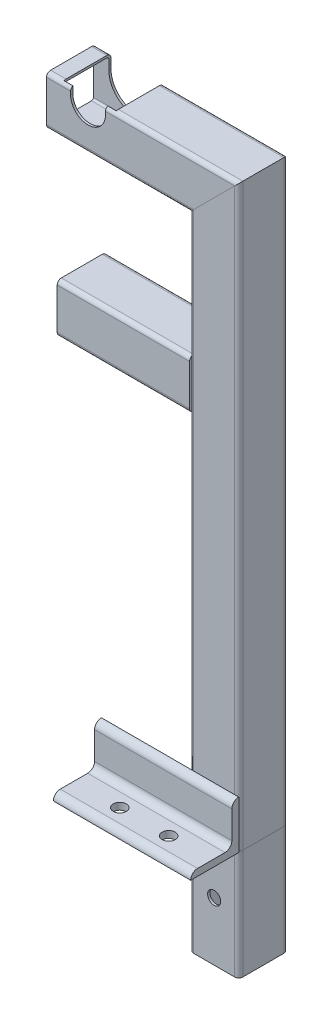
SolidWorks part; units mm, degrees
ref_plane "Front Plane" through (0, 0, 0) normal (0, 0, 1) x (1, 0, 0)
ref_plane "Top Plane" through (0, 0, 0) normal (0, 1, 0) x (1, 0, 0)
ref_plane "Right Plane" through (0, 0, 0) normal (1, 0, 0) x (0, 0, -1)
sketch "Sketch1" plane through (0, 0, 0) normal (0, 0, 1) x (1, 0, 0)
  line L0 (276.8375, 0) -> (276.8375, 404)
  line L1 (276.8375, 404) -> (154.7375, 404)
  line L2 (276.8375, 0) -> (276.8375, -80)
  line L3 (258.9375, 157.0549) -> (258.9375, -80) construction
  line L4 (263.7, 157.0549) -> (263.7, -80) construction
  line L5 (276.8375, 157.0549) -> (276.8375, -80) construction
  line L6 (276.8375, 276.9) -> (162.5375, 276.9)
  dimension "D1" = 404
  dimension "D2" = 80
  dimension "D3" = 122.1
  dimension "D4" = 4.7625
  dimension "D5" = 17.9
  dimension "D6" = 263.7
  dimension "D7" = 276.9
  dimension "D8" = 114.3
other "Structural MemberMain"
ref_plane "Plane1" through (276.8375, 0, 0) normal (0, 1, 0) x (-1, 0, 0)
sketch "Sketch11" plane through (276.8375, 0, 0) normal (0, 1, 0) x (-1, 0, 0)
  line L0 (-14.9, 16.3) -> (14.9, 16.3)
  line L1 (-14.9, 17.9) -> (14.9, 17.9)
  line L2 (-17.9, 14.9) -> (-17.9, -14.9)
  line L3 (-14.9, -17.9) -> (14.9, -17.9)
  line L4 (17.9, 14.9) -> (17.9, -14.9)
  line L5 (-17.9, 17.9) -> (17.9, -17.9) construction
  line L6 (-17.9, -17.9) -> (17.9, 17.9) construction
  line L7 (16.3, 14.9) -> (16.3, -14.9)
  line L8 (-14.9, -16.3) -> (14.9, -16.3)
  line L9 (-16.3, 14.9) -> (-16.3, -14.9)
  arc A0 (-17.9, -14.9) -> (-14.9, -17.9) centre (-14.9, -14.9) ccw
  arc A1 (14.9, -17.9) -> (17.9, -14.9) centre (14.9, -14.9) ccw
  arc A2 (17.9, 14.9) -> (14.9, 17.9) centre (14.9, 14.9) ccw
  arc A3 (-14.9, 17.9) -> (-17.9, 14.9) centre (-14.9, 14.9) ccw
  arc A4 (16.3, 14.9) -> (14.9, 16.3) centre (14.9, 14.9) ccw
  arc A5 (14.9, -16.3) -> (16.3, -14.9) centre (14.9, -14.9) ccw
  arc A6 (-16.3, -14.9) -> (-14.9, -16.3) centre (-14.9, -14.9) ccw
  arc A7 (-14.9, 16.3) -> (-16.3, 14.9) centre (-14.9, 14.9) ccw
  point P0 (0, 0)
  point P30 (0, 0)
  dimension "D3" = 3
  dimension "D1" = 35.8
  dimension "D2" = 35.8
  dimension "D4" = 1.6
sketch "Sketch12" plane through (0, 0, 0) normal (0, 0, 1) x (1, 0, 0)
  line L1 (185, 416.7) -> (185, 427.1) construction
  line L2 (172.3, 416.7) -> (172.3, 427.1)
  line L3 (197.7, 416.7) -> (197.7, 427.1)
  line L4 (276.8375, 404) -> (154.7375, 404) construction
  line L5 (154.7375, 421.9) -> (294.7375, 421.9) construction
  arc A0 (172.3, 416.7) -> (197.7, 416.7) centre (185, 416.7) ccw
  arc A1 (197.7, 427.1) -> (172.3, 427.1) centre (185, 427.1) ccw
  point P2 (185, 421.9)
  dimension "D1" = 25.4
  dimension "D2" = 185
extrude "Cut-ExtrudeTopRailGuide" cut sketch "Sketch12" against normal through all and the other way through all
sketch "Sketch13" plane through (0, 0, 0) normal (0, 1, 0) x (1, 0, 0)
  line L0 (194.7375, -17.9) -> (294.7375, -17.9)
  line L1 (197.7, -17.9) -> (291.7375, -17.9) construction
  line L3 (294.7375, 14.9) -> (294.7375, -14.9) construction
  point P4 (244.7375, -17.9)
  dimension "D1" = 100
other "Structural MemberAngle"
ref_plane "Plane2" through (194.7375, 0, 17.9) normal (1, 0, 0) x (0, 1, 0)
sketch "Sketch14" plane through (194.7375, 0, 17.9) normal (1, 0, 0) x (0, 1, 0)
  line L0 (0, 0) -> (0, 35)
  line L1 (0, 17.5) -> (5, 17.5) construction
  line L2 (5, 30) -> (5, 10)
  line L3 (10, 5) -> (30, 5)
  line L4 (17.5, 5) -> (17.5, 0) construction
  line L5 (35, 0) -> (0, 0)
  arc A0 (35, 0) -> (30, 5) centre (30, 0) ccw
  arc A1 (0, 35) -> (5, 30) centre (0, 30) cw
  arc A2 (10, 5) -> (5, 10) centre (10, 10) cw
  point P10 (17.5, 0)
  point P14 (0, 17.5)
  point P15 (5, 17.5)
  point P16 (17.5, 5)
  point P17 (5, 35)
  point P18 (35, 5)
  point P21 (0, 0)
  dimension "D2" = 5
  dimension "D3" = 35
  dimension "Radius_1" = 5
  dimension "D1" = 5
sketch "Sketch15" plane through (0, 0, 0) normal (0, 1, 0) x (1, 0, 0)
  line L0 (244.7375, -17.9) -> (244.7375, -52.9) construction
  line L1 (294.7375, -52.9) -> (194.7375, -52.9) construction
  line L2 (-65.8005, -37.9) -> (555.2755, -37.9) construction
  line L3 (194.7375, -17.9) -> (294.7375, -17.9) construction
  line L4 (0, 28.933) -> (0, -28.933) construction
  circle A0 centre (228.1, -37.9) radius 4.7625
  circle A1 centre (263.7, -37.9) radius 4.7625
  point P7 (244.7375, -37.9)
  point P16 (0, 0)
  dimension "D2" = 9.525
  dimension "D1" = 20
  dimension "D3" = 263.7
  dimension "D4" = 35.6
extrude "Cut-ExtrudeMountingHoles" cut sketch "Sketch15" along normal through all
sketch "Sketch16" plane through (0, 0, 0) normal (0, 0, 1) x (1, 0, 0)
  line L0 (185, 431.9) -> (185, 411.9) construction
  line L1 (204.1, 431.9) -> (204.1, 411.9)
  line L2 (165.9, 431.9) -> (165.9, 411.9)
  line L3 (197.7, 421.9) -> (294.7375, 421.9) construction
  arc A0 (204.1, 431.9) -> (165.9, 431.9) centre (185, 431.9) ccw
  arc A1 (165.9, 411.9) -> (204.1, 411.9) centre (185, 411.9) ccw
  point P2 (185, 421.9)
  dimension "D1" = 19.1
  dimension "D2" = 10
extrude "Cut-ExtrudeEnlargeRailGuide" cut sketch "Sketch16" against normal through all and the other way up to surface other way up to face at (200.3937, 409.3125, 16.3)
sketch "Sketch17" plane through (0, 0, 17.9) normal (0, 0, 1) x (1, 0, 0)
  line L0 (276.8375, 0) -> (276.8375, -80) construction
  line L1 (194.7375, 0) -> (294.7375, 0) construction
  line L2 (294.7375, 0) -> (294.7375, -80) construction
  circle A0 centre (276.8375, -37.5) radius 4.7625
  dimension "D1" = 9.525
  dimension "D3" = 17.9
  dimension "D2" = 37.5
extrude "Cut-Extrude1" cut sketch "Sketch17" against normal through all
